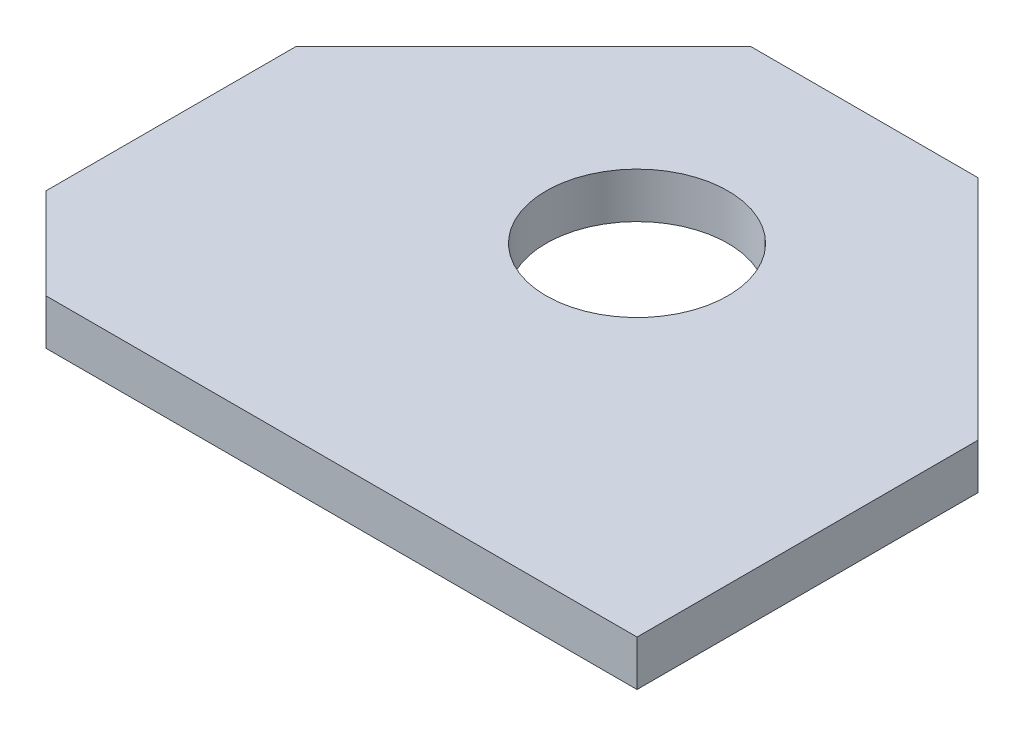
SolidWorks part; units mm, degrees
material "Alloy Steel"
ref_plane "Front Plane" through (0, 0, 0) normal (0, 0, 1) x (1, 0, 0)
ref_plane "Top Plane" through (0, 0, 0) normal (0, 1, 0) x (1, 0, 0)
ref_plane "Right Plane" through (0, 0, 0) normal (1, 0, 0) x (0, 0, -1)
sketch "Sketch1" plane through (0, 0, 0) normal (0, 1, 0) x (1, 0, 0)
  line L0 (0, 12.5) -> (0, -12.5) construction
  line L1 (5, 12.5) -> (-5, 12.5)
  line L2 (-5, 12.5) -> (-15, 2.5)
  line L3 (-15, 2.5) -> (-15, -12.5)
  line L4 (-15, -12.5) -> (15, -12.5)
  line L5 (15, 2.5) -> (15, -12.5)
  line L6 (5, 12.5) -> (15, 2.5)
  circle A0 centre (0, 2.5) radius 4
  dimension "D3" = 8
  dimension "D1" = 45
  dimension "D2" = 30
  dimension "D4" = 15
  dimension "D5" = 10
extrude "Boss-Extrude1" add sketch "Sketch1" along normal mid plane 2
chamfer "Chamfer1" distance 4 angle 45 1 edges at (-15, 0, 12.5)
